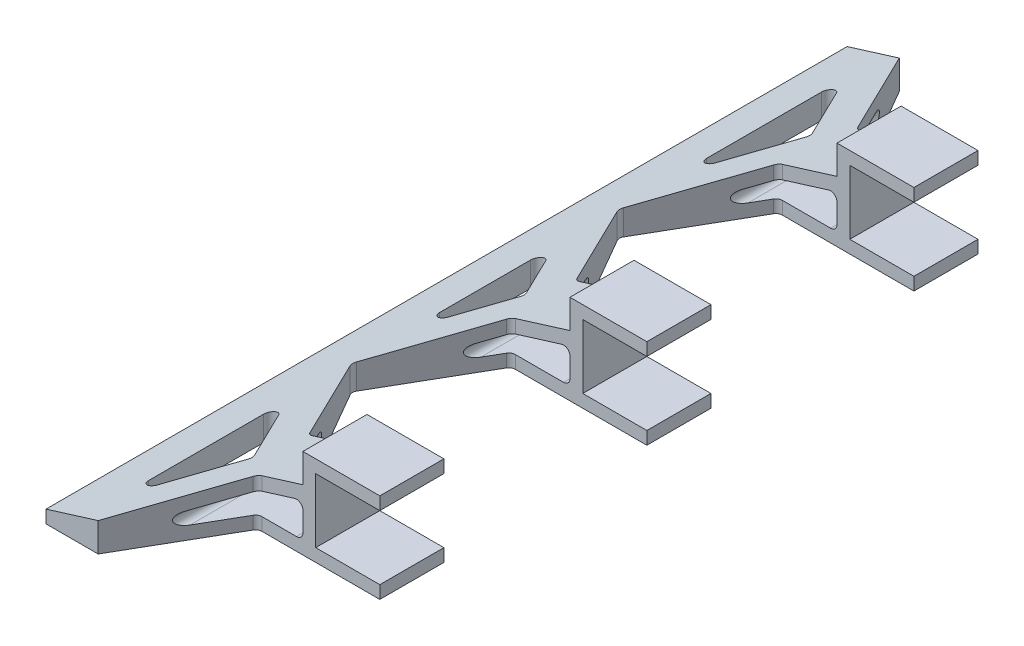
SolidWorks part; units mm, degrees
ref_plane "前视基准面" through (0, 0, 0) normal (0, 0, 1) x (1, 0, 0)
ref_plane "上视基准面" through (0, 0, 0) normal (0, 1, 0) x (1, 0, 0)
ref_plane "右视基准面" through (0, 0, 0) normal (1, 0, 0) x (0, 0, -1)
sketch "草图1" plane through (0, 0, 0) normal (1, 0, 0) x (0, 0, -1)
  line L1 (-40.6358, 16.9636) -> (209.3642, 16.9636)
  line L2 (-40.6358, 16.9636) -> (-40.6358, -11.0364)
  line L3 (-40.6358, -11.0364) -> (209.3642, -11.0364)
  line L4 (209.3642, 16.9636) -> (209.3642, -11.0364)
  line L5 (-40.6358, 12.9636) -> (209.3642, 12.9636)
  line L6 (-40.6358, 12.9636) -> (-40.6358, -7.0364)
  line L7 (-40.6358, -7.0364) -> (209.3642, -7.0364)
  line L8 (209.3642, 12.9636) -> (209.3642, -7.0364)
  dimension "D1" = 20
  dimension "D2" = 4
  dimension "D3" = 4
  dimension "D4" = 250
extrude "凸台-拉伸1" add sketch "草图1" along normal blind 20 contours L2 L5 L4 L1 | L7 L2 L3 L4
sketch "草图2" plane through (0, 0, 0) normal (-1, 0, 0) x (0, 0, 1)
  line L1 (-209.3642, 16.9636) -> (40.6358, 16.9636)
  line L2 (-209.3642, 16.9636) -> (-209.3642, -11.0364)
  line L3 (-209.3642, -11.0364) -> (40.6358, -11.0364)
  line L4 (40.6358, 16.9636) -> (40.6358, -11.0364)
extrude "凸台-拉伸2" add sketch "草图2" along normal blind 4
sketch "草图3" plane through (-4, 0, 0) normal (-1, 0, 0) x (0, 0, 1)
  line L0 (40.6358, -11.0364) -> (40.6358, 16.9636) construction
  line L1 (-209.3642, -11.0364) -> (40.6358, -11.0364)
  line L2 (-209.3642, -11.0364) -> (-209.3642, -7.0364)
  line L3 (-209.3642, -7.0364) -> (40.6358, -7.0364)
  line L4 (40.6358, -11.0364) -> (40.6358, -7.0364)
  dimension "D1" = 4
extrude "凸台-拉伸3" add sketch "草图3" along normal blind 48.5
sketch "草图5" plane through (0, 0, 40.6358) normal (0, 0, 1) x (1, 0, 0)
  line L0 (-4, -7.0364) -> (-52.5, -7.0364)
  line L1 (-52.5, -7.0364) -> (-4, 7.9636)
  line L2 (-4, -7.0364) -> (-4, 16.9636) construction
  line L3 (-4, 7.9636) -> (-4, -7.0364)
  dimension "D1" = 15
extrude "凸台-拉伸4" add sketch "草图5" against normal blind 250
ref_plane "基准面1" through (0, 0, -84.3642) normal (0, 0, -1) x (-1, 0, 0)
sketch "草图7" plane through (0, 16.9636, 0) normal (0, 1, 0) x (1, 0, 0)
  line L0 (-36.22, 209.3642) -> (-17.9373, 177.6975)
  line L1 (-4, 209.3642) -> (-52.5, 209.3642) construction
  line L2 (-17.9373, 177.6975) -> (20, 177.6975)
  line L3 (20, -40.6358) -> (20, 209.3642) construction
  line L4 (20, 177.6975) -> (20, 209.3642)
  line L5 (20, 209.3642) -> (-36.22, 209.3642)
  line L6 (20, 157.6975) -> (-22.2172, 157.6975)
  line L7 (-22.2172, 157.6975) -> (-40.5, 126.0308)
  line L8 (-40.5, 126.0308) -> (-22.2172, 94.3642)
  line L9 (-22.2172, 94.3642) -> (20, 94.3642)
  line L10 (20, 94.3642) -> (20, 157.6975)
  line L11 (-40.5, 196.7773) -> (-40.5, 146.0308)
  line L12 (-40.5, 146.0308) -> (-25.8508, 171.404)
  line L13 (-25.8508, 171.404) -> (-40.5, 196.7773)
  line L14 (-40.5, 106.0308) -> (-27.9907, 84.3642)
  line L15 (15.4, 84.3642) -> (-15.4, 84.3642) construction
  line L16 (-27.9907, 84.3642) -> (-40.5, 84.3642)
  line L17 (-40.5, 84.3642) -> (-40.5, 106.0308)
  line L18 (-52.5, -40.6358) -> (-52.5, 209.3642) construction
  point P21 (-33.1754, 184.0907)
  dimension "D1" = 10
  dimension "D2" = 10
  dimension "D3" = 10
  dimension "D4" = 60
  dimension "D5" = 120
  dimension "D6" = 30
  dimension "D7" = 120
  dimension "D8" = 12
  dimension "D9" = 12
  dimension "D10" = 20
  dimension "D11" = 10
  dimension "D12" = 31.6667
  dimension "D13" = 31.6667
extrude "切除-拉伸1" cut sketch "草图7" against normal blind 55
mirror "镜向1" about plane through (0, 0, -84.3642) normal (0, 0, -1) of "切除-拉伸1"
fillet "圆角1" radius 2 17 edges at (-40.5, -7.1808, -42.6975) (-40.5, -7.1808, -126.0308) (-17.9373, -3.6917, -177.6975) (-22.2172, -4.3535, -94.3642) (-22.2172, -4.3535, -157.6975) (-22.2172, -4.3535, -74.3642) (-17.9373, -3.6917, 8.9692) (-22.2172, -4.3535, -11.0308) (-40.5, -7.1808, 28.0489) (-40.5, -7.1808, -22.6975) (-25.8508, -4.9154, 2.6757) (-40.5, -7.1808, -62.6975) (-27.9907, -5.2464, -84.3642) (-40.5, -7.1808, -106.0308) (-40.5, -7.1808, -146.0308) (-40.5, -7.1808, -196.7773) (-25.8508, -4.9154, -171.404)
sketch "草图8" plane through (0, 0, -209.3642) normal (0, 0, -1) x (-1, 0, 0)
  line L0 (4, 1.0646) -> (4, -5.0364)
  line L1 (6, -7.0364) -> (25.7267, -7.0364)
  line L2 (26.3176, -3.1257) -> (6.5909, 2.9753)
  line L3 (16.7826, 4.0102) -> (4, 7.9636) construction
  line L4 (4, 7.9636) -> (4, 16.9636) construction
  line L5 (0, -7.0364) -> (-20, -7.0364) construction
  arc A0 (4, -5.0364) -> (6, -7.0364) centre (6, -5.0364) ccw
  arc A1 (25.7267, -7.0364) -> (26.3176, -3.1257) centre (25.7267, -5.0364) ccw
  arc A2 (4, 1.0646) -> (6.5909, 2.9753) centre (6, 1.0646) cw
  dimension "D2" = 2
  dimension "D1" = 4
extrude "切除-拉伸2" cut sketch "草图8" against normal blind 250
